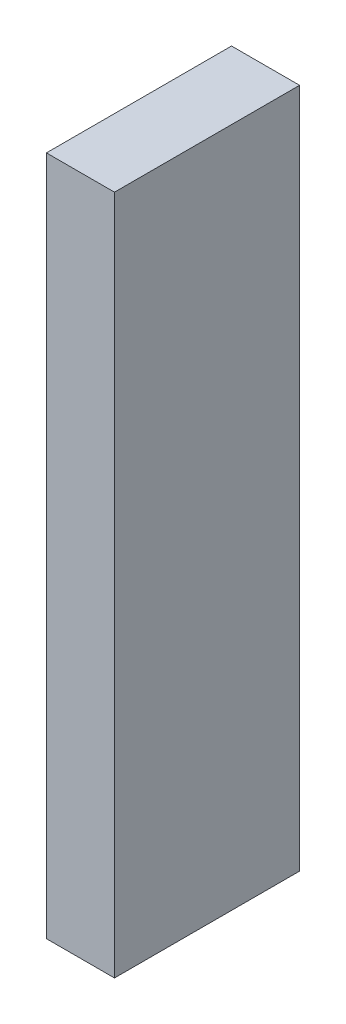
SolidWorks part; units mm, degrees
material "POLYURETHANE (11671)"
ref_plane "Front Plane" through (0, 0, 0) normal (0, 0, 1) x (1, 0, 0)
ref_plane "Top Plane" through (0, 0, 0) normal (0, 1, 0) x (1, 0, 0)
ref_plane "Right Plane" through (0, 0, 0) normal (1, 0, 0) x (0, 0, -1)
sketch "Sketch1" plane through (0, 0, 0) normal (1, 0, 0) x (0, 0, -1)
  line L1 (-4.318, -15.875) -> (4.318, -15.875)
  line L2 (-4.318, -15.875) -> (-4.318, 15.875)
  line L3 (-4.318, 15.875) -> (4.318, 15.875)
  line L4 (4.318, -15.875) -> (4.318, 15.875)
  line L5 (-4.318, -15.875) -> (4.318, 15.875) construction
  line L6 (-4.318, 15.875) -> (4.318, -15.875) construction
  point P0 (0, 0)
  dimension "D1" = 8.636
  dimension "D2" = 31.75
extrude "Boss-Extrude1" add sketch "Sketch1" along normal blind 3.175
